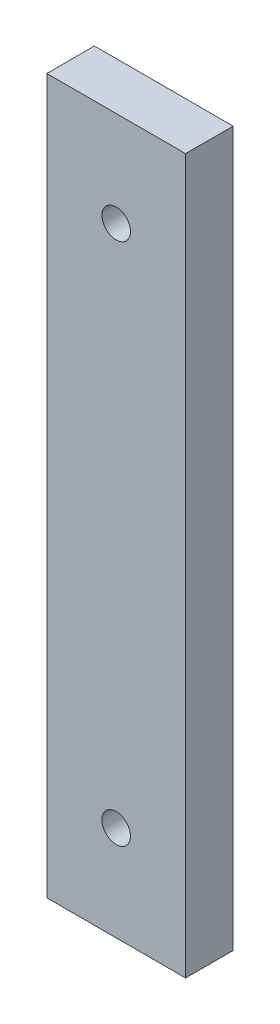
SolidWorks part; units mm, degrees
ref_plane "Front Plane" through (0, 0, 0) normal (0, 0, 1) x (1, 0, 0)
ref_plane "Top Plane" through (0, 0, 0) normal (0, 1, 0) x (1, 0, 0)
ref_plane "Right Plane" through (0, 0, 0) normal (1, 0, 0) x (0, 0, -1)
sketch "Sketch1" plane through (0, 0, 0) normal (0, 0, 1) x (1, 0, 0)
  line L0 (0, 0) -> (31.7495, 0) construction
  line L1 (-14.5788, -75) -> (14.5788, -75)
  line L2 (-14.5788, -75) -> (-14.5788, 75)
  line L3 (-14.5788, 75) -> (14.5788, 75)
  line L4 (14.5788, -75) -> (14.5788, 75)
  line L5 (-14.5788, -75) -> (14.5788, 75) construction
  line L6 (-14.5788, 75) -> (14.5788, -75) construction
  circle A0 centre (0, 55) radius 3
  circle A1 centre (0, -55) radius 3
  point P0 (0, 0)
  point P10 (0, 0)
  dimension "D3" = 6
  dimension "D4" = 6
  dimension "D1" = 150
  dimension "D2" = 110
extrude "Boss-Extrude1" add sketch "Sketch1" along normal blind 10
